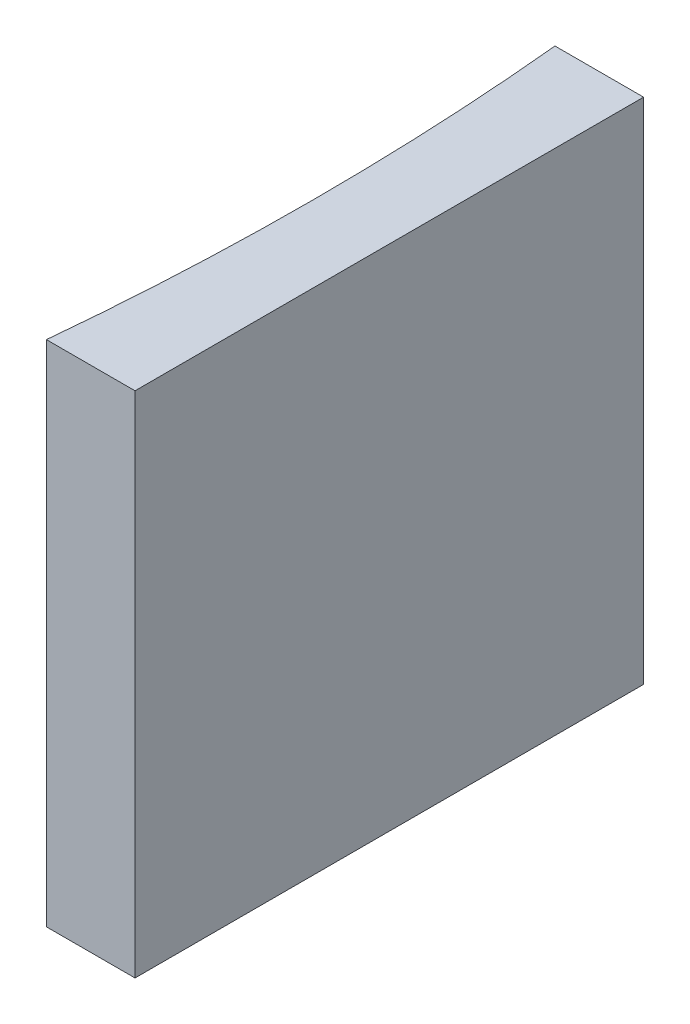
SolidWorks part; units mm, degrees
ref_plane "前视基准面" through (0, 0, 0) normal (0, 0, 1) x (1, 0, 0)
ref_plane "上视基准面" through (0, 0, 0) normal (0, 1, 0) x (1, 0, 0)
ref_plane "右视基准面" through (0, 0, 0) normal (1, 0, 0) x (0, 0, -1)
sketch "草图1" plane through (0, 0, 0) normal (0, 1, 0) x (1, 0, 0)
  line L0 (0, 0) -> (0, -20)
  line L1 (0, 0) -> (-3.4847, 0)
  line L2 (0, -20) -> (-3.4847, -20)
  line L3 (8.2336, -10) -> (-10.4405, -10) construction
  arc A0 (-3.4847, -20) -> (-3.4847, 0) centre (-106.4, -10) ccw
  point P7 (-3, -10)
  point P8 (0, -10)
  dimension "D2" = 103.4
  dimension "D3" = 3
  dimension "D1" = 20
extrude "凸台-拉伸1" add sketch "草图1" along normal blind 20
